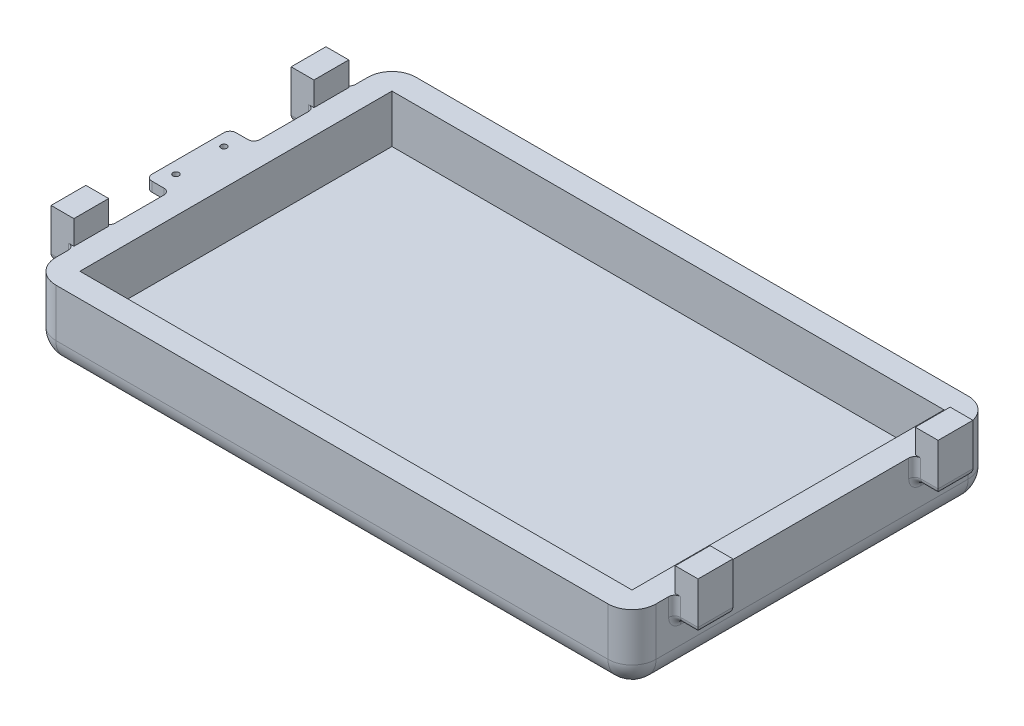
SolidWorks part; units mm, degrees
ref_plane "Front Plane" through (0, 0, 0) normal (0, 0, 1) x (1, 0, 0)
ref_plane "Top Plane" through (0, 0, 0) normal (0, 1, 0) x (1, 0, 0)
ref_plane "Right Plane" through (0, 0, 0) normal (1, 0, 0) x (0, 0, -1)
sketch "Sketch1" plane through (0, 0, 0) normal (0, 1, 0) x (1, 0, 0)
  line L1 (-125, 75) -> (125, 75)
  line L2 (-125, 75) -> (-125, -75)
  line L3 (-125, -75) -> (125, -75)
  line L4 (125, 75) -> (125, -75)
  line L5 (-125, 75) -> (125, -75) construction
  line L6 (-125, -75) -> (125, 75) construction
  point P0 (0, 0)
  dimension "D1" = 150
  dimension "D2" = 250
extrude "Boss-Extrude1" add sketch "Sketch1" along normal blind 30
sketch "Sketch2" plane through (0, 30, 0) normal (0, 1, 0) x (1, 0, 0)
  line L0 (125, -75) -> (125, 75) construction
  line L1 (-115, 65) -> (115, 65)
  line L2 (-115, 65) -> (-115, -65)
  line L3 (-115, -65) -> (115, -65)
  line L4 (115, 65) -> (115, -65)
  line L5 (-115, 65) -> (115, -65) construction
  line L6 (-115, -65) -> (115, 65) construction
  line L7 (125, 75) -> (-125, 75) construction
  point P0 (0, 0)
  dimension "D1" = 10
  dimension "D2" = 10
extrude "Cut-Extrude1" cut sketch "Sketch2" against normal blind 20 contours L1 L4 L3 L2
fillet "Fillet1" radius 10 8 edges at (0, 0, -75) (125, 15, -75) (125, 0, 0) (125, 15, 75) (-125, 15, -75) (-125, 0, 0) (0, 0, 75) (-125, 15, 75)
sketch "Sketch3" plane through (0, 30, 0) normal (0, 1, 0) x (1, 0, 0)
  line L0 (-125, 65) -> (-125, -65) construction
  line L1 (-125, 57.25) -> (-134.75, 57.25)
  line L2 (-125, 57.25) -> (-125, 42.75)
  line L3 (-125, 42.75) -> (-134.75, 42.75)
  line L4 (-134.75, 57.25) -> (-134.75, 42.75)
  line L5 (0, 0) -> (-61.3751, 0) construction
  line L6 (0, 0) -> (0, -39.9844) construction
  line L7 (-134.75, -57.25) -> (-134.75, -42.75)
  line L8 (-125, -42.75) -> (-134.75, -42.75)
  line L9 (-125, -57.25) -> (-125, -42.75)
  line L10 (-125, -57.25) -> (-134.75, -57.25)
  line L11 (125, -57.25) -> (134.75, -57.25)
  line L12 (125, -57.25) -> (125, -42.75)
  line L13 (125, -42.75) -> (134.75, -42.75)
  line L14 (134.75, -57.25) -> (134.75, -42.75)
  line L15 (134.75, 57.25) -> (134.75, 42.75)
  line L16 (125, 42.75) -> (134.75, 42.75)
  line L17 (125, 57.25) -> (125, 42.75)
  line L18 (125, 57.25) -> (134.75, 57.25)
  point P6 (-125, 50)
  dimension "D1" = 50
  dimension "D2" = 14.5
  dimension "D3" = 9.75
extrude "Boss-Extrude2" add sketch "Sketch3" along normal blind 10 and the other way blind 10
fillet "Fillet3" radius 2.5 24 edges at (125, 25, -57.25) (125, 25, -42.75) (125, 25, 57.25) (125, 25, 42.75) (-125, 25, 57.25) (-125, 25, 42.75) (-125, 25, -57.25) (-125, 25, -42.75) (125, 20, -50) (129.875, 20, -42.75) (134.75, 20, -50) (129.875, 20, -57.25) (129.875, 20, 57.25) (129.875, 20, 42.75) (134.75, 20, 50) (125, 20, 50) (-134.75, 20, 50) (-129.875, 20, 57.25) (-125, 20, 50) (-129.875, 20, 42.75) (-129.875, 20, -57.25) (-129.875, 20, -42.75) (-134.75, 20, -50) (-125, 20, -50)
sketch "Sketch4" plane through (0, 30, 0) normal (0, 1, 0) x (1, 0, 0)
  line L0 (-125, -57.25) -> (-125, -42.75) construction
  line L1 (-125.25, 67.7652) -> (125.25, 67.7652)
  line L2 (-125.25, 67.7652) -> (-125.25, -67.7652)
  line L3 (-125.25, -67.7652) -> (125.25, -67.7652)
  line L4 (125.25, 67.7652) -> (125.25, -67.7652)
  line L5 (-125.25, 67.7652) -> (125.25, -67.7652) construction
  line L6 (-125.25, -67.7652) -> (125.25, 67.7652) construction
  point P0 (0, 0)
  dimension "D1" = 0.25
extrude "Cut-Extrude3" cut sketch "Sketch4" along normal blind 36
sketch "Sketch5" plane through (0, 30, 0) normal (0, 1, 0) x (1, 0, 0)
  line L0 (-125, 40.25) -> (-125, -40.25) construction
  line L1 (-125, 17.5) -> (-135, 17.5)
  line L2 (-125, 17.5) -> (-125, -17.5)
  line L3 (-125, -17.5) -> (-135, -17.5)
  line L4 (-135, 17.5) -> (-135, -17.5)
  line L5 (-135, 0) -> (-125, 0) construction
  circle A0 centre (-130, 10) radius 1.25
  circle A1 centre (-130, -10) radius 1.25
  point P6 (-125, 0)
  dimension "D3" = 2.5
  dimension "D1" = 35
  dimension "D2" = 10
  dimension "D4" = 10
  dimension "D5" = 5
extrude "Boss-Extrude5" add sketch "Sketch5" against normal blind 4
fillet "Fillet4" radius 2.5 4 edges at (-125, 28, 17.5) (-135, 28, 17.5) (-125, 28, -17.5) (-135, 28, -17.5)
